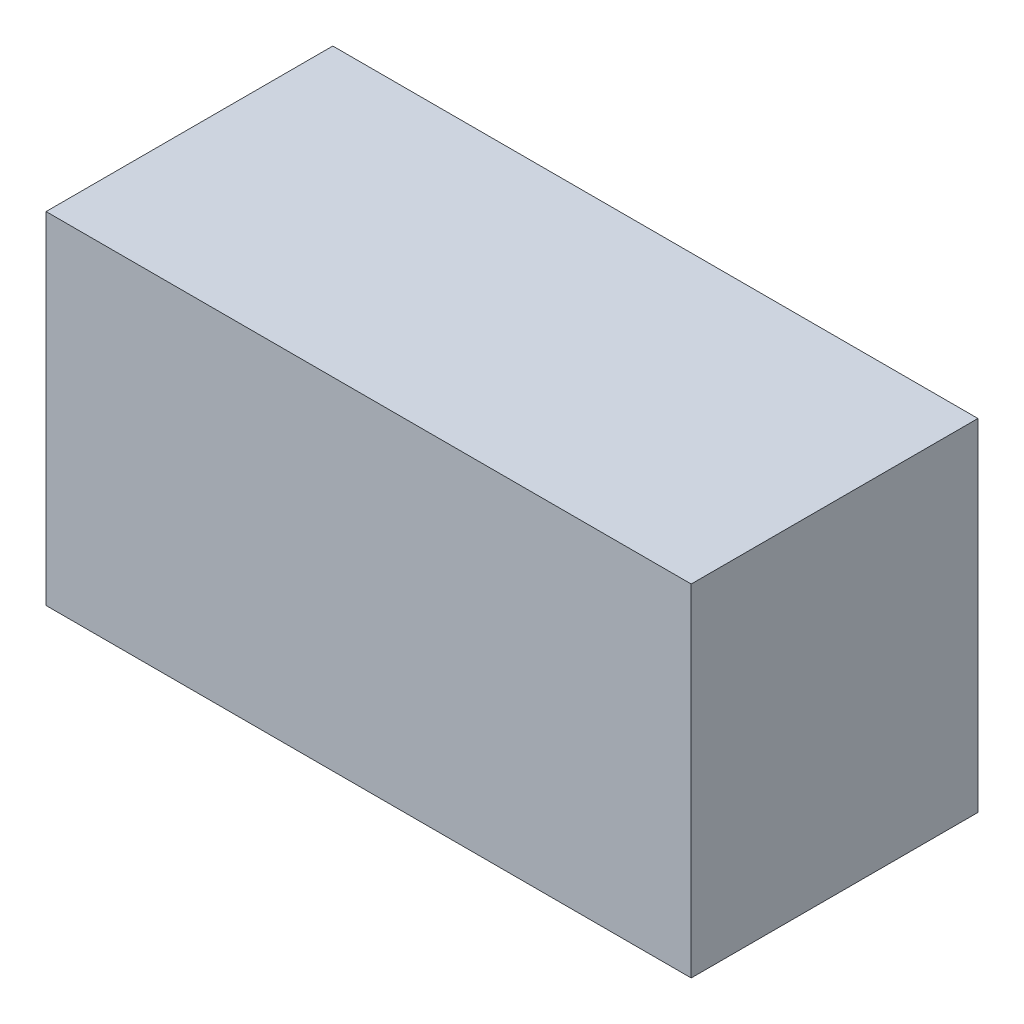
SolidWorks part; units mm, degrees
ref_plane "Front Plane" through (0, 0, 0) normal (0, 0, 1) x (1, 0, 0)
ref_plane "Top Plane" through (0, 0, 0) normal (0, 1, 0) x (1, 0, 0)
ref_plane "Right Plane" through (0, 0, 0) normal (1, 0, 0) x (0, 0, -1)
sketch "Sketch1" plane through (0, 0, 0) normal (0, 0, 1) x (1, 0, 0)
  line L1 (-11.25, 5.95) -> (11.25, 5.95)
  line L2 (-11.25, 5.95) -> (-11.25, -5.95)
  line L3 (-11.25, -5.95) -> (11.25, -5.95)
  line L4 (11.25, 5.95) -> (11.25, -5.95)
  line L5 (-11.25, 5.95) -> (11.25, -5.95) construction
  line L6 (-11.25, -5.95) -> (11.25, 5.95) construction
  point P0 (0, 0)
  dimension "D1" = 11.9
  dimension "D2" = 22.5
extrude "Boss-Extrude1" add sketch "Sketch1" along normal mid plane 10
sketch "Sketch2" plane through (0, 0, -5) normal (0, 0, -1) x (-1, 0, 0)
  circle A0 centre (0, 0) radius 1.5
  dimension "D1" = 3
extrude "Boss-Extrude2" add sketch "Sketch2" along normal blind 4
